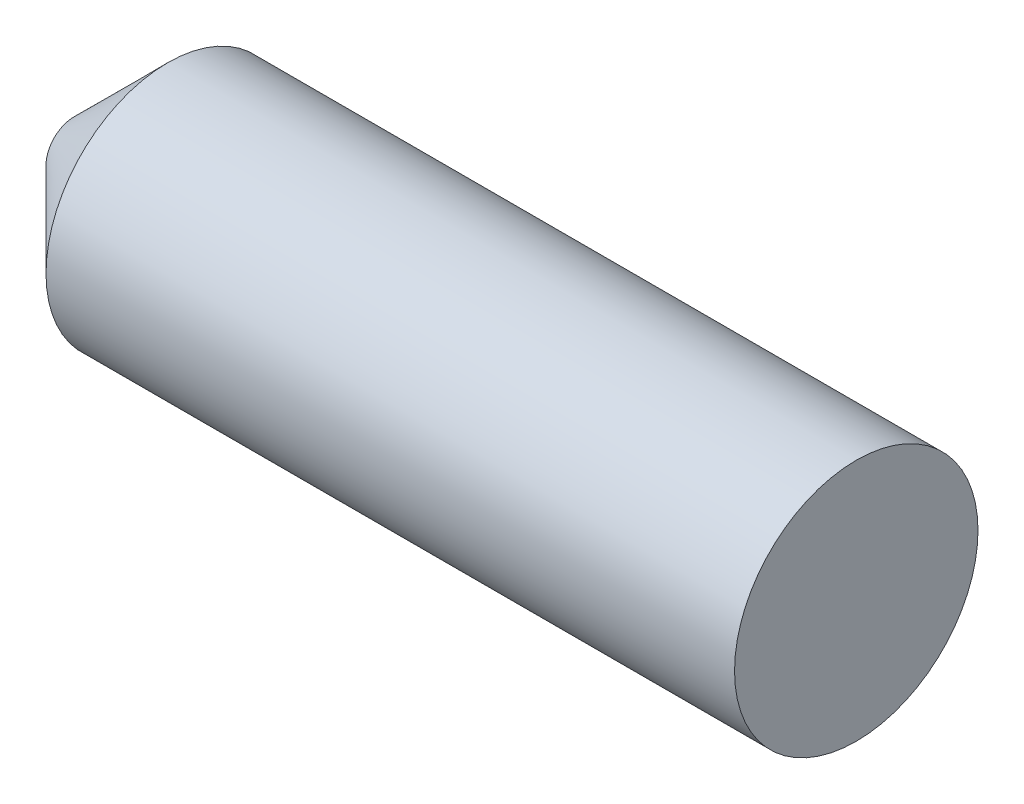
SolidWorks part; units mm, degrees
ref_plane "Front Plane" through (0, 0, 0) normal (0, 0, 1) x (1, 0, 0)
ref_plane "Top Plane" through (0, 0, 0) normal (0, 1, 0) x (1, 0, 0)
ref_plane "Right Plane" through (0, 0, 0) normal (1, 0, 0) x (0, 0, -1)
sketch "Sketch1" plane through (0, 0, 0) normal (1, 0, 0) x (0, 0, -1)
  circle A0 centre (0, 0) radius 24.765
extrude "Boss-Extrude1" add sketch "Sketch1" along normal blind 121.031
sketch "Sketch3" plane through (0, 0, 0) normal (-1, 0, 0) x (0, 0, 1)
  circle A0 centre (0, 0) radius 24.765
extrude "Boss-Extrude2" add sketch "Sketch3" along normal blind 38.1
chamfer "Chamfer1" distance 19.05 angle 45 1 edges at (-38.1, 0, 24.765)
